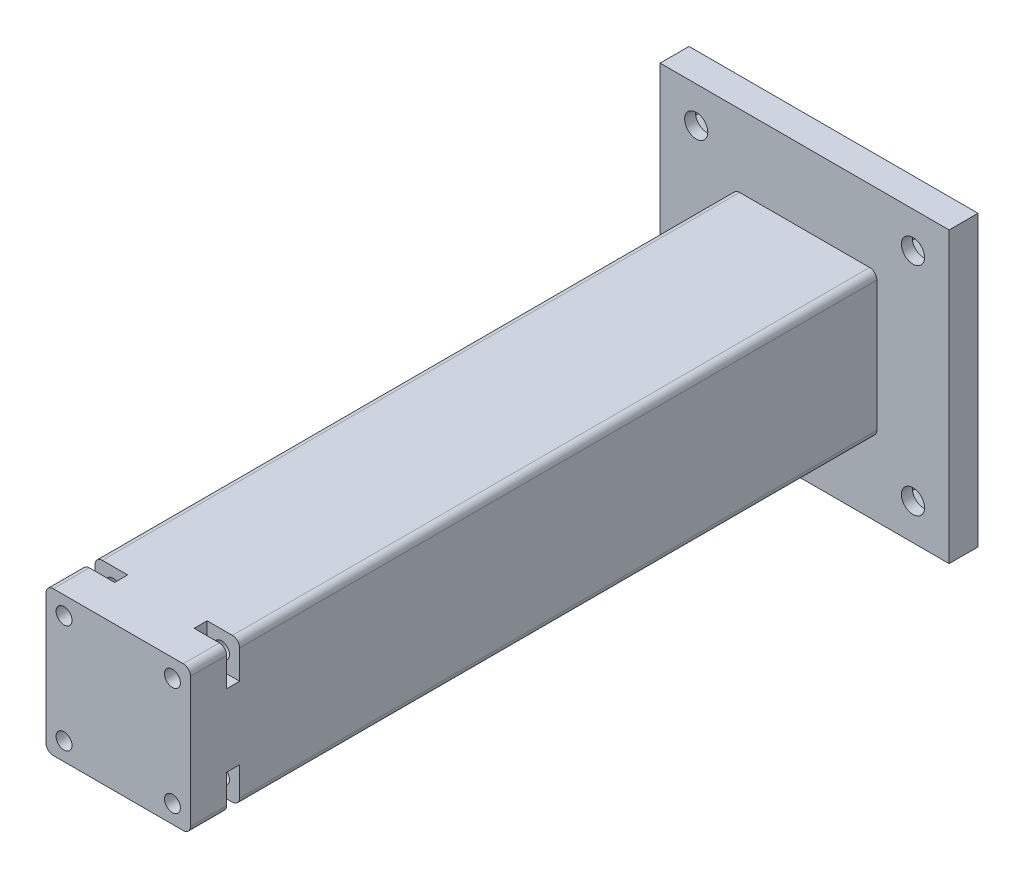
SolidWorks part; units mm, degrees
ref_plane "Plan de face" through (0, 0, 0) normal (0, 0, 1) x (1, 0, 0)
ref_plane "Plan de dessus" through (0, 0, 0) normal (0, 1, 0) x (1, 0, 0)
ref_plane "Plan de droite" through (0, 0, 0) normal (1, 0, 0) x (0, 0, -1)
sketch "Esquisse1" plane through (0, 0, 0) normal (0, 0, 1) x (1, 0, 0)
  line L1 (-20, 20) -> (20, 20)
  line L2 (-20, 20) -> (-20, -20)
  line L3 (-20, -20) -> (20, -20)
  line L4 (20, 20) -> (20, -20)
  dimension "D1" = 20
  dimension "D2" = 40
  dimension "D3" = 20
  dimension "D4" = 40
extrude "Boss.-Extru.1" add sketch "Esquisse1" along normal blind 4
sketch "Esquisse4" plane through (0, 0, 4) normal (0, 0, 1) x (1, 0, 0)
  line L1 (-10, 10) -> (10, 10)
  line L2 (-10, 10) -> (-10, -10)
  line L3 (-10, -10) -> (10, -10)
  line L4 (10, 10) -> (10, -10)
  point P4 (0, 0)
  dimension "D1" = 10
  dimension "D2" = 20
  dimension "D3" = 10
  dimension "D4" = 20
extrude "Boss.-Extru.4" add sketch "Esquisse4" along normal blind 95
fillet "Congé3" radius 1 4 edges at (-10, 10, 51.5) (10, 10, 51.5) (-10, -10, 51.5) (10, -10, 51.5)
sketch "Esquisse5" plane through (0, 0, 99) normal (0, 0, 1) x (1, 0, 0)
  line L0 (9, 10) -> (-9, 10) construction
  line L1 (-10, 9) -> (-10, -9) construction
  line L2 (10, -9) -> (10, 9) construction
  line L3 (-9, -10) -> (9, -10) construction
  circle A0 centre (7.5, 7.5) radius 1.1
  circle A1 centre (-7.5, 7.5) radius 1.1
  circle A2 centre (-7.5, -7.5) radius 1.1
  circle A3 centre (7.5, -7.5) radius 1.1
  dimension "D1" = 2.2
  dimension "D2" = 2.5
  dimension "D3" = 2.5
  dimension "D4" = 2.5
  dimension "D5" = 2.5
extrude "Enlèv. mat.-Extru.1" cut sketch "Esquisse5" against normal blind 20
sketch "Esquisse6" plane through (0, -10, 0) normal (0, -1, 0) x (1, 0, 0)
  line L0 (-9, 99) -> (9, 99) construction
  line L1 (-10, 94) -> (-5.5, 94)
  line L2 (-10, 94) -> (-10, 92.2)
  line L3 (-10, 92.2) -> (-5.5, 92.2)
  line L4 (-5.5, 94) -> (-5.5, 92.2)
  line L5 (10, 94) -> (5.5, 94)
  line L6 (10, 94) -> (10, 92.2)
  line L7 (10, 92.2) -> (5.5, 92.2)
  line L8 (5.5, 94) -> (5.5, 92.2)
  line L9 (-10, 4) -> (-10, 99) construction
  line L10 (10, 99) -> (10, 4) construction
  dimension "D2" = 5
  dimension "D3" = 1.8
  dimension "D5" = 4.5
  dimension "D6" = 4.5
extrude "Enlèv. mat.-Extru.2" cut sketch "Esquisse6" against normal blind 5
mirror "Symétrie1" about plane through (0, 0, 0) normal (0, 1, 0) of "Enlèv. mat.-Extru.2"
sketch "Esquisse7" plane through (0, 0, 0) normal (0, 0, -1) x (-1, 0, 0)
  line L0 (20, 20) -> (20, -20) construction
  line L1 (-20, -20) -> (-20, 20) construction
  line L2 (20, -20) -> (-20, -20) construction
  line L3 (-20, 20) -> (20, 20) construction
  line L4 (-9, 10) -> (9, 10) construction
  line L5 (10, 9) -> (10, -9) construction
  circle A0 centre (15, 15) radius 1.6
  circle A1 centre (15, -15) radius 1.6
  circle A2 centre (-15, -15) radius 1.6
  circle A3 centre (-15, 15) radius 1.6
  dimension "D1" = 3.2
  dimension "D2" = 5
  dimension "D3" = 5
  dimension "D4" = 5
  dimension "D5" = 5
  dimension "D6" = 5
  dimension "D7" = 5
extrude "Enlèv. mat.-Extru.3" cut sketch "Esquisse7" against normal up to surface (4 mm away) up to face at (0, 0, 4)
sketch "Esquisse8" plane through (0, 0, 0) normal (0, 0, -1) x (-1, 0, 0)
  line L0 (-20, -20) -> (-20, 20) construction
  line L1 (-11.9689, 13.25) -> (-11.9689, 16.75)
  line L2 (-11.9689, 16.75) -> (-15, 18.5)
  line L3 (-15, 18.5) -> (-18.0311, 16.75)
  line L4 (-18.0311, 16.75) -> (-18.0311, 13.25)
  line L5 (-18.0311, 13.25) -> (-15, 11.5)
  line L6 (-15, 11.5) -> (-11.9689, 13.25)
  line L7 (15, 11.5) -> (18.0311, 13.25)
  line L8 (18.0311, 13.25) -> (18.0311, 16.75)
  line L9 (18.0311, 16.75) -> (15, 18.5)
  line L10 (15, 18.5) -> (11.9689, 16.75)
  line L11 (11.9689, 16.75) -> (11.9689, 13.25)
  line L12 (11.9689, 13.25) -> (15, 11.5)
  line L13 (15, -18.5) -> (18.0311, -16.75)
  line L14 (18.0311, -16.75) -> (18.0311, -13.25)
  line L15 (18.0311, -13.25) -> (15, -11.5)
  line L16 (15, -11.5) -> (11.9689, -13.25)
  line L17 (11.9689, -13.25) -> (11.9689, -16.75)
  line L18 (11.9689, -16.75) -> (15, -18.5)
  line L19 (-11.9689, -16.75) -> (-11.9689, -13.25)
  line L20 (-11.9689, -13.25) -> (-15, -11.5)
  line L21 (-15, -11.5) -> (-18.0311, -13.25)
  line L22 (-18.0311, -13.25) -> (-18.0311, -16.75)
  line L23 (-18.0311, -16.75) -> (-15, -18.5)
  line L24 (-15, -18.5) -> (-11.9689, -16.75)
  line L25 (20, 20) -> (20, -20) construction
  circle A0 centre (-15, 15) radius 3.0311 construction
  circle A1 centre (15, 15) radius 3.0311 construction
  circle A2 centre (15, -15) radius 3.0311 construction
  circle A3 centre (-15, -15) radius 3.0311 construction
  dimension "D1" = 3.5
  dimension "D2" = 3.5
  dimension "D3" = 3.5
  dimension "D4" = 3.5
extrude "Enlèv. mat.-Extru.4" cut sketch "Esquisse8" against normal blind 2.5
